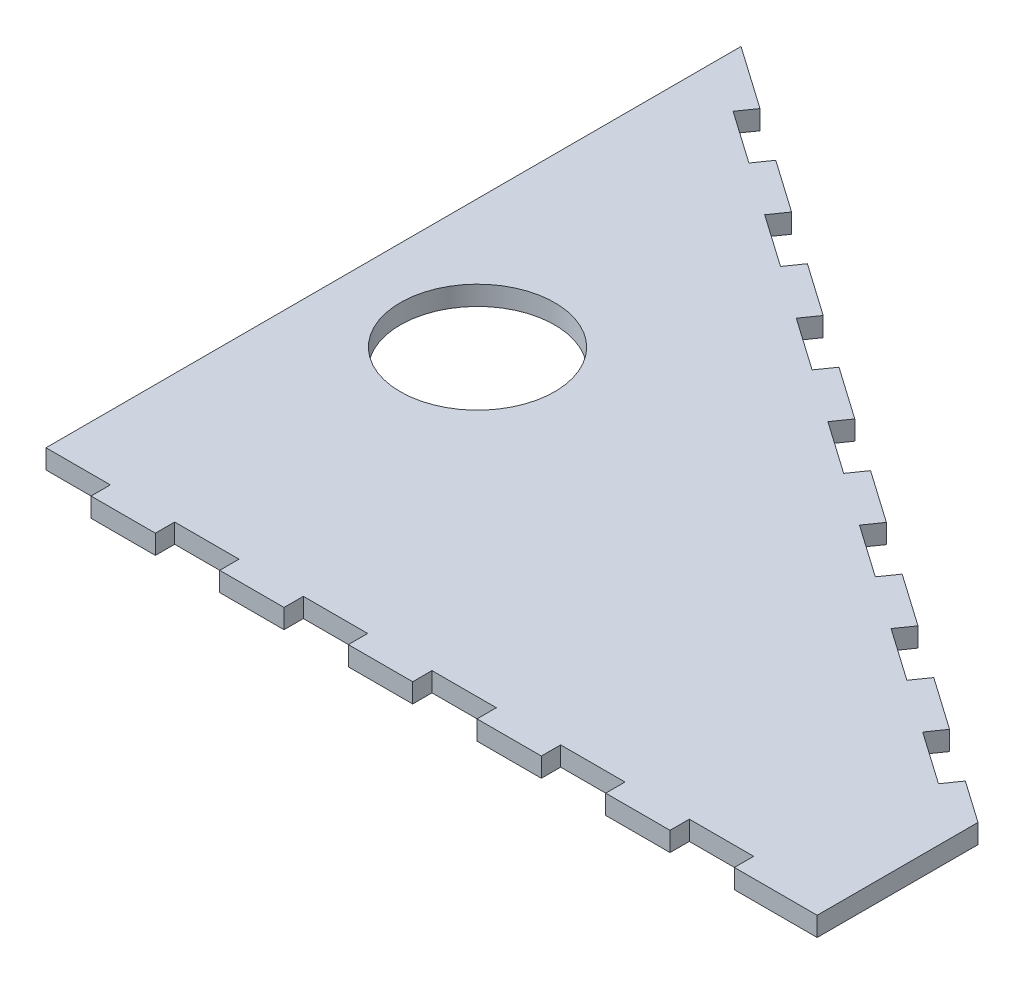
SolidWorks part; units mm, degrees
ref_plane "Plan de face" through (0, 0, 0) normal (0, 0, 1) x (1, 0, 0)
ref_plane "Plan de dessus" through (0, 0, 0) normal (0, 1, 0) x (1, 0, 0)
ref_plane "Plan de droite" through (0, 0, 0) normal (1, 0, 0) x (0, 0, -1)
sketch "Esquisse1" plane through (0, 0, 0) normal (0, 1, 0) x (1, 0, 0)
  line L0 (0, 0) -> (122.8728, 0) construction
  line L1 (0, 0) -> (0, 86.0365)
  line L2 (0, 86.0365) -> (122.8728, 0) construction
  line L3 (9.8298, 79.1535) -> (8.1091, 76.6961)
  line L4 (8.1091, 76.6961) -> (16.3006, 70.9603)
  line L5 (16.3006, 70.9603) -> (18.0213, 73.4178)
  line L6 (9.8298, 79.1535) -> (18.0213, 73.4178) construction
  line L7 (26.2129, 67.682) -> (34.4044, 61.9463) construction
  line L8 (32.6837, 59.4888) -> (34.4044, 61.9463)
  line L9 (24.4921, 65.2246) -> (32.6837, 59.4888)
  line L10 (26.2129, 67.682) -> (24.4921, 65.2246)
  line L11 (42.5959, 56.2105) -> (50.7874, 50.4747) construction
  line L12 (49.0667, 48.0173) -> (50.7874, 50.4747)
  line L13 (40.8752, 53.753) -> (49.0667, 48.0173)
  line L14 (42.5959, 56.2105) -> (40.8752, 53.753)
  line L15 (58.9789, 44.739) -> (67.1705, 39.0032) construction
  line L16 (65.4497, 36.5457) -> (67.1705, 39.0032)
  line L17 (57.2582, 42.2815) -> (65.4497, 36.5457)
  line L18 (58.9789, 44.739) -> (57.2582, 42.2815)
  line L19 (75.362, 33.2674) -> (83.5535, 27.5317) construction
  line L20 (81.8328, 25.0742) -> (83.5535, 27.5317)
  line L21 (73.6413, 30.81) -> (81.8328, 25.0742)
  line L22 (75.362, 33.2674) -> (73.6413, 30.81)
  line L23 (91.745, 21.7959) -> (99.9365, 16.0601) construction
  line L24 (98.2158, 13.6027) -> (99.9365, 16.0601)
  line L25 (90.0243, 19.3384) -> (98.2158, 13.6027)
  line L26 (91.745, 21.7959) -> (90.0243, 19.3384)
  line L27 (108.1281, 10.3244) -> (116.3196, 4.5886) construction
  line L28 (114.5989, 2.1312) -> (116.3196, 4.5886)
  line L29 (106.4073, 7.8669) -> (114.5989, 2.1312)
  line L30 (108.1281, 10.3244) -> (106.4073, 7.8669)
  line L31 (0, 86.0365) -> (9.8298, 79.1535)
  line L32 (0, 0) -> (122.8728, 0) construction
  line L33 (0, 0) -> (0, -22)
  line L34 (10, -25) -> (20, -25)
  line L35 (122.8728, 0) -> (122.8728, -25)
  line L36 (18.0213, 73.4178) -> (26.2129, 67.682)
  line L37 (34.4044, 61.9463) -> (42.5959, 56.2105)
  line L38 (50.7874, 50.4747) -> (58.9789, 44.739)
  line L39 (67.1705, 39.0032) -> (75.362, 33.2674)
  line L40 (83.5535, 27.5317) -> (91.745, 21.7959)
  line L41 (99.9365, 16.0601) -> (108.1281, 10.3244)
  line L42 (116.3196, 4.5886) -> (122.8728, 0)
  line L43 (20, -25) -> (20, -22)
  line L46 (0, -22) -> (10, -22)
  line L47 (10, -25) -> (10, -22)
  line L49 (30, -25) -> (30, -22)
  line L50 (20, -22) -> (30, -22)
  line L51 (40, -25) -> (40, -22)
  line L53 (50, -25) -> (50, -22)
  line L54 (40, -22) -> (50, -22)
  line L55 (60, -25) -> (60, -22)
  line L57 (70, -25) -> (70, -22)
  line L58 (60, -22) -> (70, -22)
  line L59 (80, -25) -> (80, -22)
  line L61 (90, -25) -> (90, -22)
  line L62 (80, -22) -> (90, -22)
  line L63 (100, -25) -> (100, -22)
  line L65 (110, -25) -> (110, -22)
  line L66 (100, -22) -> (110, -22)
  line L67 (30, -25) -> (40, -25)
  line L68 (50, -25) -> (60, -25)
  line L69 (70, -25) -> (80, -25)
  line L70 (90, -25) -> (100, -25)
  line L71 (110, -25) -> (122.8728, -25)
  circle A0 centre (20, 25.0742) radius 12
  dimension "D8" = 24
  dimension "D1" = 35
  dimension "D2" = 150
  dimension "D3" = 12
  dimension "D4" = 10
  dimension "D5" = 3
  dimension "D7" = 25
  dimension "D9" = 10
  dimension "D10" = 3
  dimension "D6" = 7
  dimension "D11" = 6
extrude "Boss.-Extru.1" add sketch "Esquisse1" along normal blind 3
